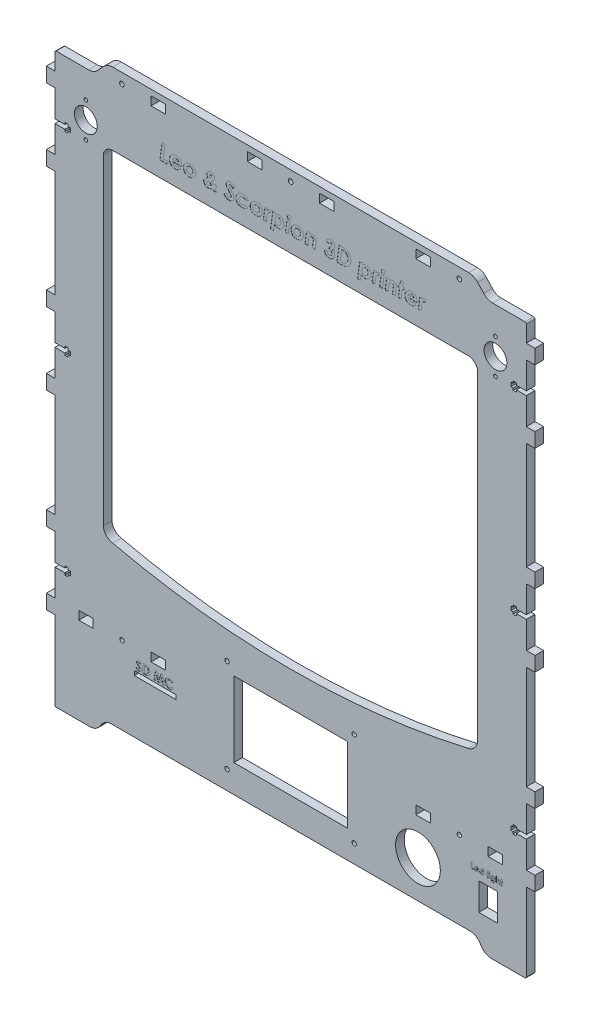
SolidWorks part; units mm, degrees
ref_plane "Спереди" through (0, 0, 0) normal (0, 0, 1) x (1, 0, 0)
ref_plane "Сверху" through (0, 0, 0) normal (0, 1, 0) x (1, 0, 0)
ref_plane "Справа" through (0, 0, 0) normal (1, 0, 0) x (0, 0, -1)
sketch "Эскиз1" plane through (0, 0, 0) normal (0, 0, 1) x (1, 0, 0)
  line L0 (-95.8892, 197.3491) -> (-85.8892, 197.3491)
  line L1 (-85.8892, 197.3491) -> (-85.8892, 191.3491)
  line L2 (-85.8892, 191.3491) -> (-95.8892, 191.3491)
  line L3 (-95.8892, 191.3491) -> (-95.8892, 197.3491)
  line L4 (97.3908, 191.3491) -> (87.3908, 191.3491)
  line L5 (87.3908, 191.3491) -> (87.3908, 197.3491)
  line L6 (87.3908, 197.3491) -> (97.3908, 197.3491)
  line L7 (97.3908, 197.3491) -> (97.3908, 191.3491)
  line L8 (97.3654, -141.9477) -> (87.3654, -141.9477)
  line L9 (87.3654, -141.9477) -> (87.3654, -135.9477)
  line L10 (87.3654, -135.9477) -> (97.3654, -135.9477)
  line L11 (97.3654, -135.9477) -> (97.3654, -141.9477)
  line L12 (147.3854, -141.9477) -> (137.3854, -141.9477)
  line L13 (137.3854, -141.9477) -> (137.3854, -135.9477)
  line L14 (137.3854, -135.9477) -> (147.3854, -135.9477)
  line L15 (147.3854, -135.9477) -> (147.3854, -141.9477)
  line L16 (-135.8946, -141.9477) -> (-145.8946, -141.9477)
  line L17 (-145.8946, -141.9477) -> (-145.8946, -135.9477)
  line L18 (-145.8946, -135.9477) -> (-135.8946, -135.9477)
  line L19 (-135.8946, -135.9477) -> (-135.8946, -141.9477)
  line L20 (-85.8746, -141.9477) -> (-95.8746, -141.9477)
  line L21 (-95.8746, -141.9477) -> (-95.8746, -135.9477)
  line L22 (-95.8746, -135.9477) -> (-85.8746, -135.9477)
  line L23 (-85.8746, -135.9477) -> (-85.8746, -141.9477)
  line L24 (-19.2392, 191.3491) -> (-29.2392, 191.3491)
  line L25 (-29.2392, 191.3491) -> (-29.2392, 197.3491)
  line L26 (-29.2392, 197.3491) -> (-19.2392, 197.3491)
  line L27 (-19.2392, 197.3491) -> (-19.2392, 191.3491)
  line L28 (30.7408, 191.3491) -> (20.7408, 191.3491)
  line L29 (20.7408, 191.3491) -> (20.7408, 197.3491)
  line L30 (20.7408, 197.3491) -> (30.7408, 197.3491)
  line L31 (30.7408, 197.3491) -> (30.7408, 191.3491)
  line L32 (-122.3991, 151.3491) -> (123.6241, 151.3491)
  line L33 (40.0454, -173.6357) -> (40.0454, -121.6361)
  line L34 (40.0454, -121.6361) -> (-38.5546, -121.6361)
  line L35 (-38.5546, -121.6361) -> (-38.5546, -173.6357)
  line L36 (-38.5546, -173.6357) -> (40.0454, -173.6357)
  line L37 (143.9388, -159.6762) -> (143.9388, -178.6762)
  line L38 (143.9388, -178.6762) -> (130.9388, -178.6762)
  line L39 (130.9388, -178.6762) -> (130.9388, -159.6762)
  line L40 (130.9388, -159.6762) -> (143.9388, -159.6762)
  line L41 (-162.3492, -146.9309) -> (-168.3546, -146.9309)
  line L42 (-168.3546, -146.9309) -> (-168.3546, -136.9309)
  line L43 (-168.3546, -136.9309) -> (-162.3546, -136.9309)
  line L44 (-162.3546, -136.9309) -> (-162.3546, -118.3209)
  line L45 (-162.3546, -96.9409) -> (-168.3546, -96.9409)
  line L46 (-168.3546, -96.9409) -> (-168.3546, -86.9409)
  line L47 (-168.3546, -86.9409) -> (-162.3546, -86.9409)
  line L48 (-162.3546, -86.9409) -> (-162.3546, -15.2109)
  line L49 (-162.3546, -15.2109) -> (-168.3546, -15.2109)
  line L50 (-162.3546, 34.7891) -> (-168.3546, 34.7891)
  line L51 (-168.3546, -5.2109) -> (-162.3546, -5.2109)
  line L52 (-168.3546, 44.7891) -> (-162.3546, 44.7891)
  line L56 (-162.3546, 128.9491) -> (-162.3546, 147.5491)
  line L57 (-162.3492, 168.9491) -> (-168.3492, 168.9491)
  line L58 (-168.3492, 168.9491) -> (-168.3492, 178.9491)
  line L59 (-168.3492, 178.9491) -> (-162.3492, 178.9491)
  line L60 (-162.3492, 178.9491) -> (-162.3492, 190.3491)
  line L61 (-162.3492, -200.9709) -> (-162.3492, -146.9309)
  line L62 (163.8454, -146.9309) -> (169.8454, -146.9309)
  line L63 (169.8454, -146.9309) -> (169.8454, -136.9309)
  line L64 (169.8454, -136.9309) -> (163.8513, -136.9309)
  line L65 (163.8513, -136.9309) -> (163.8513, -118.3209)
  line L66 (163.9392, -96.9409) -> (169.8512, -96.9409)
  line L67 (169.8512, -96.9409) -> (169.8512, -86.9409)
  line L68 (169.8512, -86.9409) -> (163.8512, -86.9409)
  line L69 (163.8512, -86.9409) -> (163.8512, -15.2109)
  line L70 (163.8512, -15.2109) -> (169.8512, -15.2109)
  line L71 (163.8512, 34.7891) -> (169.8512, 34.7891)
  line L72 (169.8512, -5.2109) -> (163.8512, -5.2109)
  line L73 (169.8512, 44.7891) -> (163.8512, 44.7891)
  line L74 (163.8512, 118.9491) -> (169.8512, 118.9491)
  line L75 (169.8512, 118.9491) -> (169.8512, 128.9491)
  line L76 (169.8512, 128.9491) -> (163.8512, 128.9491)
  line L77 (163.8512, 128.9491) -> (163.8512, 147.5491)
  line L78 (163.8508, 168.9491) -> (169.8508, 168.9491)
  line L79 (169.8508, 168.9491) -> (169.8508, 178.9491)
  line L80 (169.8508, 178.9491) -> (163.8508, 178.9491)
  line L81 (163.8508, 178.9491) -> (163.8508, 190.3491)
  line L82 (156.9388, 150.3491) -> (156.9388, 151.7492)
  line L83 (163.9392, -115.5209) -> (156.9392, -115.5209)
  line L84 (156.9392, -114.1224) -> (154.7382, -114.1224)
  line L85 (156.9399, -118.3209) -> (163.8513, -118.3209)
  line L86 (153.2384, -118.3222) -> (154.7405, -118.3222)
  line L87 (-155.4441, 11.989) -> (-153.2432, 11.989)
  line L88 (154.7382, -114.1224) -> (154.7382, -115.5222)
  line L89 (154.7391, 16.1893) -> (153.24, 16.1893)
  line L90 (153.2384, -115.5222) -> (153.2384, -118.3222)
  line L91 (-155.4426, -119.721) -> (-153.2418, -119.721)
  line L92 (163.8508, 150.3491) -> (156.9388, 150.3491)
  line L93 (156.9399, -119.7231) -> (156.9399, -118.3209)
  line L94 (156.9392, -115.5209) -> (156.9392, -114.1224)
  line L95 (154.7382, -115.5222) -> (153.2384, -115.5222)
  line L96 (154.741, 147.5502) -> (154.741, 146.1493)
  line L97 (-155.4451, -114.1209) -> (-155.4451, -115.5209)
  line L98 (154.7415, 13.3902) -> (154.7415, 11.9893)
  line L99 (-162.3546, 147.5491) -> (-155.4441, 147.5491)
  line L100 (-155.4441, 147.5491) -> (-155.4441, 146.149)
  line L101 (-155.4398, 150.3491) -> (-162.3492, 150.3491)
  line L102 (-153.2398, 150.3482) -> (-153.2398, 151.7491)
  line L103 (154.7405, -118.3222) -> (154.7405, -119.7231)
  line L104 (-155.4451, -115.5209) -> (-162.3546, -115.5209)
  line L105 (154.741, 151.7492) -> (154.741, 150.3493)
  line L106 (156.9417, 146.1493) -> (156.9417, 147.5491)
  line L107 (-153.2432, 13.3622) -> (-151.7428, 13.3622)
  line L108 (-155.4426, -118.3209) -> (-155.4426, -119.721)
  line L109 (153.241, 150.3493) -> (153.241, 147.5502)
  line L110 (-153.2451, 17.5891) -> (-155.4451, 17.5891)
  line L111 (-162.3546, 13.3891) -> (-155.4441, 13.3891)
  line L112 (154.741, 146.1493) -> (156.9417, 146.1493)
  line L113 (153.241, 147.5502) -> (154.741, 147.5502)
  line L114 (-153.2433, 147.5489) -> (-151.7375, 147.5489)
  line L115 (-151.7428, 13.3622) -> (-151.7428, 16.1885)
  line L116 (163.8512, 16.1891) -> (156.9392, 16.1891)
  line L117 (154.7391, 17.5621) -> (154.7391, 16.1893)
  line L118 (154.741, 150.3493) -> (153.241, 150.3493)
  line L119 (154.7415, 11.9893) -> (156.9417, 11.9893)
  line L120 (-153.2451, -114.1209) -> (-155.4451, -114.1209)
  line L121 (-151.7436, -118.3211) -> (-151.7436, -115.5218)
  line L122 (-153.2418, -118.3211) -> (-151.7436, -118.3211)
  line L123 (-153.2432, 11.989) -> (-153.2432, 13.3622)
  line L124 (156.9417, 13.3891) -> (163.8512, 13.3891)
  line L125 (-162.3546, -118.3209) -> (-155.4426, -118.3209)
  line L126 (153.24, 16.1893) -> (153.24, 13.3902)
  line L127 (-153.2451, -115.5218) -> (-153.2451, -114.1209)
  line L128 (-151.7428, 16.1885) -> (-153.2451, 16.1885)
  line L129 (-155.4441, 146.149) -> (-153.2433, 146.149)
  line L130 (-153.2418, -119.721) -> (-153.2418, -118.3211)
  line L131 (-155.4398, 151.7491) -> (-155.4398, 150.3491)
  line L132 (-151.7436, -115.5218) -> (-153.2451, -115.5218)
  line L133 (-153.2433, 146.149) -> (-153.2433, 147.5489)
  line L134 (153.24, 13.3902) -> (154.7415, 13.3902)
  line L135 (156.9388, 151.7492) -> (154.741, 151.7492)
  line L136 (-151.7375, 147.5489) -> (-151.738, 150.3482)
  line L137 (156.9417, 147.5491) -> (163.8512, 147.5491)
  line L138 (-155.4451, 16.1891) -> (-162.3546, 16.1891)
  line L139 (156.9417, 11.9893) -> (156.9417, 13.3891)
  line L140 (-155.4451, 17.5891) -> (-155.4451, 16.1891)
  line L141 (154.7405, -119.7231) -> (156.9399, -119.7231)
  line L142 (-153.2398, 151.7491) -> (-155.4398, 151.7491)
  line L143 (156.9392, 17.5621) -> (154.7391, 17.5621)
  line L144 (-151.738, 150.3482) -> (-153.2398, 150.3482)
  line L145 (-162.3546, -115.5209) -> (-162.3546, -96.9409)
  line L146 (-162.3492, 150.3491) -> (-162.3492, 168.9491)
  line L147 (163.9392, -115.5209) -> (163.9392, -96.9409)
  line L148 (163.8508, 150.3491) -> (163.8508, 168.9491)
  line L149 (-139.0924, 191.3491) -> (-161.5253, 191.3491)
  line L150 (-128.7242, 198.5879) -> (-132.8221, 194.1104)
  line L151 (123.9554, 201.3491) -> (-122.4539, 201.3491)
  line L152 (130.2257, 198.5879) -> (134.3236, 194.1104)
  line L153 (140.5939, 191.3491) -> (162.8508, 191.3491)
  line L154 (-131.8015, -198.9146) -> (-129.7448, -195.8949)
  line L155 (162.7628, -201.9477) -> (139.7264, -201.9477)
  line L156 (133.303, -198.9146) -> (131.2463, -195.8949)
  line L157 (-161.4373, -201.9509) -> (-138.3129, -201.9509)
  line L158 (-123.2334, -192.8586) -> (124.7349, -192.8586)
  line L159 (163.8454, -200.9731) -> (163.8454, -146.9309)
  line L160 (-162.3546, 13.3891) -> (-162.3546, -5.2109)
  line L161 (-168.3546, -15.2109) -> (-168.3546, -5.2109)
  line L162 (-168.3546, 34.7891) -> (-168.3546, 44.7891)
  line L163 (-162.3546, 44.7891) -> (-162.3546, 118.9491)
  line L164 (163.8512, 13.3891) -> (163.8512, -5.2109)
  line L165 (169.8512, -15.2109) -> (169.8512, -5.2109)
  line L166 (169.8512, 34.7891) -> (169.8512, 44.7891)
  line L167 (163.8512, 44.7891) -> (163.8512, 118.9491)
  line L168 (-155.4441, 13.3891) -> (-155.4441, 11.989)
  line L169 (-153.2451, 16.1885) -> (-153.2451, 17.5891)
  line L170 (156.9392, 16.1891) -> (156.9392, 17.5621)
  line L171 (-162.3546, 34.7891) -> (-162.3546, 16.1891)
  line L172 (163.8512, 34.7891) -> (163.8512, 16.1891)
  line L173 (-107.5042, -155.9271) -> (-107.5042, -152.9271)
  line L174 (-107.5042, -152.9271) -> (-78.5042, -152.9271)
  line L175 (-78.5042, -152.9271) -> (-78.5042, -155.9271)
  line L176 (-78.5042, -155.9271) -> (-107.5042, -155.9271)
  line L177 (-162.3546, 128.9491) -> (-168.3546, 128.9491)
  line L178 (-162.3546, 118.9491) -> (-168.3546, 118.9491)
  line L179 (-168.3546, 118.9491) -> (-168.3546, 128.9491)
  line L180 (-155.4426, -141.9477) -> (156.9399, -141.9477) construction
  line L181 (-140.9992, 144.3414) -> (-140.9992, 175.9536) construction
  line L182 (142.5008, 178.9491) -> (142.5008, 143.1493) construction
  line L183 (130.1588, 145.3729) -> (130.1254, -76.9742)
  line L184 (-128.9341, 145.3729) -> (-128.9472, -76.974)
  arc A0 (-122.4711, -84.0153) -> (123.6489, -84.0153) centre (0.5889, 449.8336) ccw
  circle A3 centre (44.7454, -115.1361) radius 1.5
  circle A4 centre (44.7454, -180.3857) radius 1.5
  circle A5 centre (-43.2546, -179.8825) radius 1.5
  circle A6 centre (-43.2546, -115.1361) radius 1.5
  circle A7 centre (88.8454, -166.9477) radius 15.5
  arc A8 (130.1588, 145.3729) -> (123.6241, 151.3491) centre (123.6241, 144.7884) ccw
  arc A9 (-122.3991, 151.3491) -> (-128.9341, 145.3729) centre (-122.472, 144.8677) ccw
  arc A10 (-128.9472, -76.974) -> (-122.4711, -84.0153) centre (-121.245, -76.3888) ccw
  arc A11 (123.6489, -84.0153) -> (130.1254, -76.9742) centre (121.7477, -75.7674) ccw
  circle A12 centre (0.7508, 194.3491) radius 1.6
  circle A13 centre (-116.0492, 194.3491) radius 1.6
  arc A14 (134.3236, 194.1104) -> (140.5939, 191.3491) centre (140.5939, 199.8491) ccw
  arc A15 (-161.5253, 191.3491) -> (-162.3492, 190.3491) centre (-161.4373, 190.4372) ccw
  arc A16 (-139.0924, 191.3491) -> (-132.8221, 194.1104) centre (-139.0924, 199.8491) ccw
  arc A17 (-122.4539, 201.3491) -> (-128.7242, 198.5879) centre (-122.4539, 192.8491) ccw
  circle A18 centre (117.5508, 194.3491) radius 1.6
  arc A19 (130.2257, 198.5879) -> (123.9554, 201.3491) centre (123.9554, 192.8491) ccw
  arc A20 (163.8508, 190.3491) -> (162.8508, 191.3491) centre (162.8508, 190.3491) ccw
  arc A21 (-123.2334, -192.8586) -> (-129.7448, -195.8949) centre (-123.2334, -201.3586) ccw
  arc A22 (-138.3129, -201.9509) -> (-131.8015, -198.9146) centre (-138.3129, -193.4509) ccw
  arc A23 (131.2463, -195.8949) -> (124.7349, -192.8586) centre (124.7349, -201.3586) ccw
  arc A24 (133.303, -198.9146) -> (139.7264, -201.9477) centre (139.7677, -193.542) ccw
  arc A25 (-162.3492, -200.9709) -> (-161.4373, -201.9509) centre (-161.3926, -200.9949) ccw
  arc A26 (162.7628, -201.9477) -> (163.8454, -200.9731) centre (162.8028, -200.9035) ccw
  circle A27 centre (-140.9992, 160.3491) radius 7.9
  circle A28 centre (142.5008, 160.3491) radius 7.9
  circle A29 centre (-115.9946, -138.9477) radius 1.5
  circle A30 centre (117.4854, -138.9477) radius 1.5
  circle A31 centre (-140.9992, 172.3491) radius 1.25
  circle A32 centre (-140.9992, 148.3491) radius 1.25
  circle A33 centre (142.5008, 172.3491) radius 1.25
  circle A34 centre (142.5008, 148.3491) radius 1.25
  point P239 (87.3908, 194.3491)
  point P241 (-162.3492, 184.6491)
  dimension "D11" = 15.8
  dimension "D12" = 15.8
  dimension "D53" = 31
  dimension "D88" = 283.5
  dimension "D115" = 2.5
  dimension "D113" = 2.5
  dimension "D116" = 12
  dimension "D117" = 12
  dimension "D118" = 2.5
  dimension "D119" = 2.5
  dimension "D120" = 12
  dimension "D121" = 12
  dimension "D1" = 10
  dimension "D2" = 12.4
  dimension "D3" = 12.4
  dimension "D4" = 10
  dimension "D5" = 18.6
  dimension "D6" = 2.8
  dimension "D7" = 18.6
  dimension "D8" = 10
  dimension "D9" = 10
  dimension "D10" = 10
  dimension "D13" = 6
  dimension "D14" = 18.6
  dimension "D15" = 18.6
  dimension "D16" = 10
  dimension "D17" = 74.16
  dimension "D18" = 74.16
  dimension "D19" = 10
  dimension "D20" = 10
  dimension "D21" = 18.6
  dimension "D22" = 18.6
  dimension "D23" = 18.6
  dimension "D24" = 18.6
  dimension "D25" = 10
  dimension "D26" = 10
  dimension "D27" = 71.73
  dimension "D28" = 71.73
  dimension "D29" = 10
  dimension "D30" = 10
  dimension "D31" = 18.58
  dimension "D32" = 18.58
  dimension "D33" = 18.61
  dimension "D34" = 18.61
  dimension "D35" = 10
  dimension "D36" = 10
  dimension "D37" = 54.04
  dimension "D38" = 54.0422
  dimension "D39" = 403.2968
  dimension "D40" = 2.8
  dimension "D41" = 2.8
  dimension "D42" = 2.8
  dimension "D43" = 2.8
  dimension "D44" = 403.3
  dimension "D45" = 10
  dimension "D46" = 10
  dimension "D47" = 10
  dimension "D48" = 169.1
  dimension "D49" = 10
  dimension "D50" = 10
  dimension "D51" = 10
  dimension "D52" = 10
  dimension "D54" = 338.2
  dimension "D55" = 169.1
  dimension "D56" = 10
  dimension "D57" = 52.3
  dimension "D58" = 52.3
  dimension "D59" = 72.46
  dimension "D60" = 72.46
  dimension "D61" = 56.65
  dimension "D62" = 56.65
  dimension "D63" = 19.99
  dimension "D64" = 19.99
  dimension "D65" = 21.35
  dimension "D66" = 21.35
  dimension "D67" = 22.46
  dimension "D68" = 22.46
  dimension "D69" = 19.9
  dimension "D70" = 19.9
  dimension "D71" = 20.12
  dimension "D72" = 20.12
  dimension "D73" = 47.32
  dimension "D74" = 78.6
  dimension "D75" = 47.32
  dimension "D76" = 4.7
  dimension "D77" = 4.7
  dimension "D78" = 4.7
  dimension "D79" = 4.7
  dimension "D80" = 6.5
  dimension "D81" = 6.5
  dimension "D82" = 6
  dimension "D83" = 60
  dimension "D84" = 55.02
  dimension "D85" = 6
  dimension "D86" = 29
  dimension "D87" = 3
  dimension "D89" = 4
  dimension "D90" = 7
  dimension "D91" = 6
  dimension "D92" = 4
  dimension "D93" = 6
  dimension "D94" = 7
  dimension "D95" = 4
  dimension "D96" = 6
  dimension "D97" = 4
  dimension "D98" = 2.8
  dimension "D99" = 7
  dimension "D100" = 31
  dimension "D101" = 31
  dimension "D102" = 166.56
  dimension "D103" = 131.73
  dimension "D104" = 51.9996
  dimension "D105" = 6
  dimension "D106" = 3
  dimension "D107" = 6
  dimension "D108" = 3
  dimension "D109" = 6
  dimension "D110" = 25
  dimension "D111" = 6
  dimension "D112" = 75
  dimension "D114" = 326.2
  dimension "D122" = 50
  dimension "D123" = 13
  dimension "D124" = 19
extrude "Бобышка-Вытянуть2" add sketch "Эскиз1" along normal blind 6 contours A5 | A4 | A3 | A13 | A12 | A7 | A6 | L32 A8 L183 A11 A0 A10 L184 A9 | A18 | A30 | A29 | A28 | A27 | L4 L5 L6 L7 | L0 L1 L2 L3 | L20 L21 L22 L23 | L16 L17 L18 L19 | L12 L13 L14 L15 | L8 L9 L10 L11 | L37 L38 L39 L40 | L33 L34 L35 L36 | L28 L29 L30 L31 | L24 L25 L26 L27 | L41 L42 L43 L44 L125 L108 L91 L130 L122 L121 L132 L127 L120 L97 L104 L145 L45 L46 L47 L48 L49 L161 L51 L160 L111 L168 L87 L123 L107 L115 L128 L169 L110 L140 L138 L171 L50 L162 L52 L163 L178 L179 L177 L56 L99 L100 L129 L133 L114 L136 L144 L102 L142 L131 L101 L146 L57 L58 L59 L60 A15 L149 A16 L150 A17 L151 A19 L152 A14 L153 A20 L81 L80 L79 L78 L148 L92 L82 L135 L105 L118 L109 L113 L96 L112 L106 L137 L77 L76 L75 L74 L167 L73 L166 L71 L172 L116 L170 L143 L117 L89 L126 L134 L98 L119 L139 L124 L164 L72 L165 L70 L69 L68 L67 L66 L147 L83 L94 L84 L88 L95 L90 L86 L103 L141 L93 L85 L65 L64 L63 L62 L159 A26 L155 A24 L156 A23 L158 A21 L154 A22 L157 A25 L61 | L173 L174 L175 L176 | A32 | A31 | A33 | A34
sketch "Эскиз2" plane through (0, 0, 6) normal (0, 0, 1) x (1, 0, 0)
  line L0 (-90.3522, 162.0224) -> (97.3655, 162.0224) construction
  text T0 "<b><i>Leo & Scorpion 3D printer</i></b>" font "Century Gothic" height 11
extrude "Вырез-Вытянуть1" cut sketch "Эскиз2" against normal blind 0.1
sketch "Эскиз3" plane through (0, 0, 6) normal (0, 0, 1) x (1, 0, 0)
  line L0 (-107.2394, -151.5718) -> (-78.6482, -151.5718) construction
  text T0 "<b>SD MC</b>" font "Century Gothic" height 6
extrude "Вырез-Вытянуть2" cut sketch "Эскиз3" against normal blind 0.1
sketch "Эскиз4" plane through (0, 0, 6) normal (0, 0, 1) x (1, 0, 0)
  line L0 (124.0715, -154.8104) -> (149.0052, -154.8104) construction
  text T0 "<b>Led light</b>" font "Century Gothic" height 4
extrude "Вырез-Вытянуть3" cut sketch "Эскиз4" against normal blind 0.1
